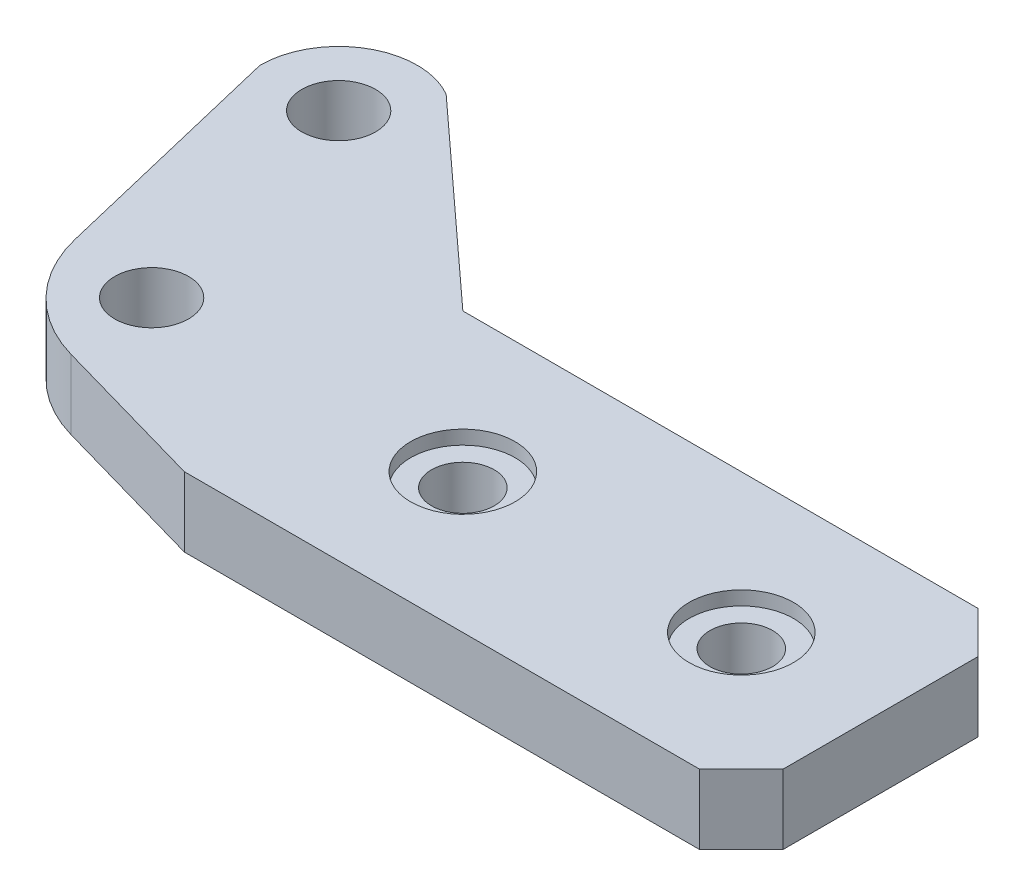
SolidWorks part; units mm, degrees
ref_plane "Front Plane" through (0, 0, 0) normal (0, 0, 1) x (1, 0, 0)
ref_plane "Top Plane" through (0, 0, 0) normal (0, 1, 0) x (1, 0, 0)
ref_plane "Right Plane" through (0, 0, 0) normal (1, 0, 0) x (0, 0, -1)
sketch "Sketch1" plane through (0, 0, 0) normal (0, 1, 0) x (1, 0, 0)
  line L0 (0, 0) -> (0, 10) construction
  line L5 (-12, -0.3526) -> (-16.9176, 18) construction
  line L6 (0, 10) -> (40, 10)
  line L10 (0, -10) -> (40, -10)
  line L11 (40, 10) -> (40, -10)
  line L12 (-12, -0.3526) -> (0, -0.3526) construction
  line L15 (-16.9176, 18) -> (-14.0926, 22.893) construction
  line L16 (-14.0926, 22.893) -> (0, 10)
  line L17 (0, 10) -> (0, -10) construction
  line L18 (-22.5676, 18) -> (-17.0168, -5.1646)
  line L19 (-17.0168, -5.1646) -> (0, -10)
  circle A2 centre (-16.9176, 18) radius 2.65
  circle A3 centre (-12, -0.3526) radius 2.65
  arc A4 (-14.0926, 22.893) -> (-22.5676, 18) centre (-16.9176, 18) ccw
  dimension "D5" = 20
  dimension "D4" = 8
  dimension "D6" = 5.3
  dimension "D7" = 5.3
  dimension "D8" = 3
  dimension "D9" = 6
  dimension "D11" = 12
  dimension "D13" = 135
  dimension "D10" = 19
  dimension "D1" = 10
  dimension "D2" = 20
  dimension "D3" = 40
  dimension "D12" = 105
  dimension "D14" = 6
extrude "Boss-Extrude1" add sketch "Sketch1" along normal blind 5
sketch "Sketch3" plane through (0, 5, 0) normal (0, 1, 0) x (1, 0, 0)
  line L0 (0, 0) -> (40, 0) construction
  line L1 (40, -10) -> (40, 10) construction
  circle A0 centre (10, 0) radius 2.25
  circle A1 centre (30, 0) radius 2.25
  dimension "D1" = 4.5
  dimension "D2" = 10
  dimension "D4" = 20
  dimension "D3" = 2
extrude "Cut-Extrude2" cut sketch "Sketch3" against normal up to next
fillet "Fillet1" radius 10 1 edges at (-17.0168, 2.5, 5.1646)
sketch "Sketch4" plane through (0, 5, 0) normal (0, 1, 0) x (1, 0, 0)
  circle A0 centre (10, 0) radius 3.75
  circle A1 centre (30, 0) radius 3.75
  dimension "D1" = 7.5
  dimension "D2" = 2
  dimension "D3" = 20
extrude "Cut-Extrude3" cut sketch "Sketch4" against normal blind 1
chamfer "Chamfer1" distance 3 angle 45 2 edges at (40, 2.5, 10) (40, 2.5, -10)
